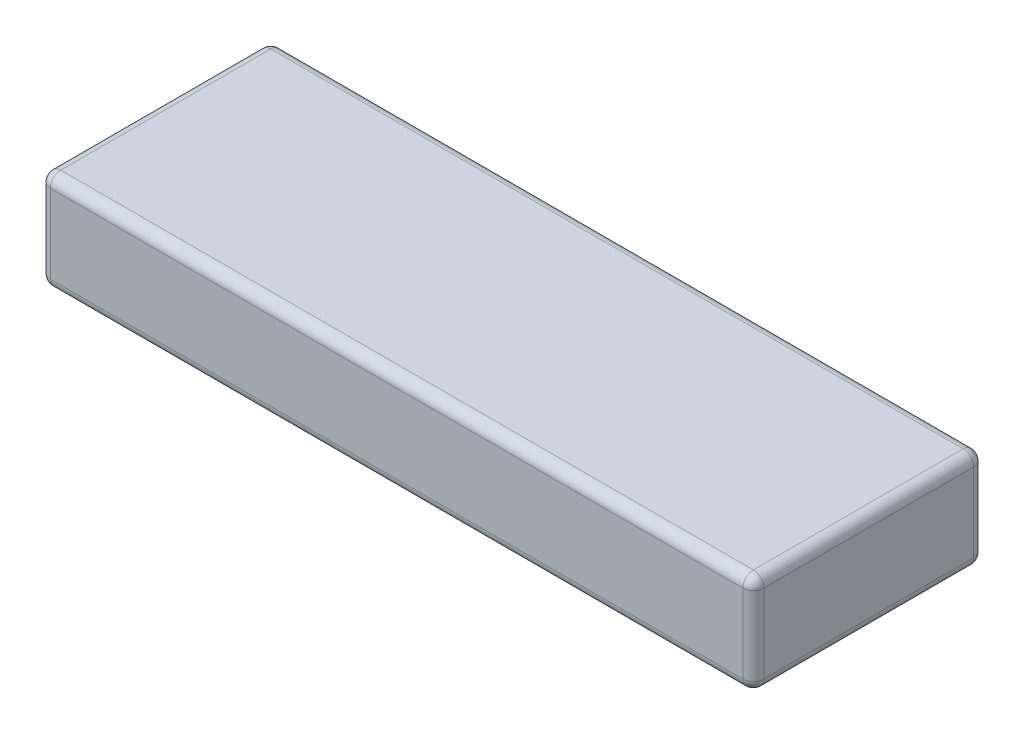
SolidWorks part; units mm, degrees
ref_plane "Front Plane" through (0, 0, 0) normal (0, 0, 1) x (1, 0, 0)
ref_plane "Top Plane" through (0, 0, 0) normal (0, 1, 0) x (1, 0, 0)
ref_plane "Right Plane" through (0, 0, 0) normal (1, 0, 0) x (0, 0, -1)
sketch "Sketch1" plane through (0, 0, 0) normal (0, 1, 0) x (1, 0, 0)
  line L1 (-68, -22) -> (68, -22)
  line L2 (-68, -22) -> (-68, 22)
  line L3 (-68, 22) -> (68, 22)
  line L4 (68, -22) -> (68, 22)
  line L5 (-68, -22) -> (68, 22) construction
  line L6 (-68, 22) -> (68, -22) construction
  point P0 (0, 0)
  dimension "D1" = 136
  dimension "D2" = 44
extrude "Boss-Extrude1" add sketch "Sketch1" along normal blind 19
fillet "Fillet1" radius 2 12 edges at (-68, 19, 0) (-68, 0, 0) (0, 19, -22) (-68, 9.5, -22) (0, 0, -22) (68, 19, 0) (68, 9.5, -22) (68, 0, 0) (-68, 9.5, 22) (0, 19, 22) (68, 9.5, 22) (0, 0, 22)
